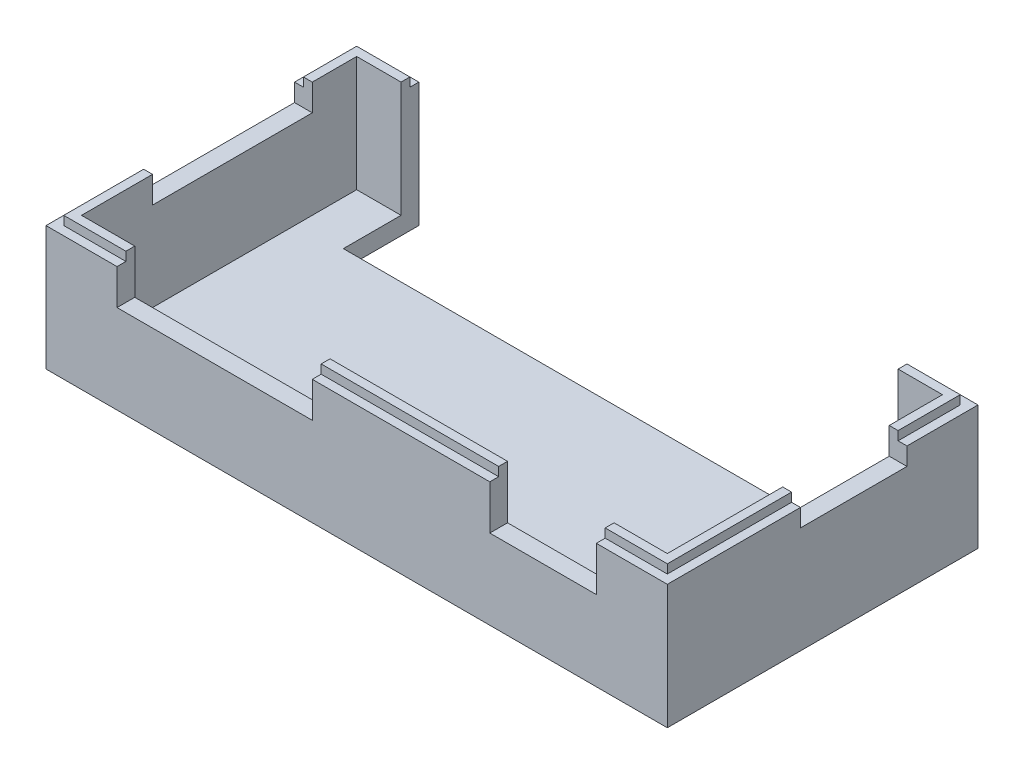
SolidWorks part; units mm, degrees
ref_plane "Front Plane" through (0, 0, 0) normal (0, 0, 1) x (1, 0, 0)
ref_plane "Top Plane" through (0, 0, 0) normal (0, 1, 0) x (1, 0, 0)
ref_plane "Right Plane" through (0, 0, 0) normal (1, 0, 0) x (0, 0, -1)
sketch "Sketch1" plane through (0, 0, 0) normal (0, 1, 0) x (1, 0, 0)
  line L0 (0, 0) -> (70, 0)
  line L1 (70, 0) -> (70, 35)
  line L2 (70, 35) -> (0, 35)
  line L3 (0, 35) -> (0, 0)
  dimension "D1" = 70
  dimension "D2" = 35
extrude "Boss-Extrude1" add sketch "Sketch1" along normal blind 2
sketch "Sketch2" plane through (0, 2, 0) normal (0, 1, 0) x (1, 0, 0)
  line L0 (68, 33) -> (2, 33)
  line L1 (2, 33) -> (2, 2)
  line L2 (2, 2) -> (68, 2)
  line L3 (68, 2) -> (68, 33)
  line L4 (0, 35) -> (0, 0)
  line L5 (0, 0) -> (70, 0)
  line L6 (70, 0) -> (70, 35)
  line L7 (70, 35) -> (0, 35)
  line L8 (0, 35) -> (0, 0)
  line L9 (0, 0) -> (70, 0)
  line L10 (70, 0) -> (70, 35)
  line L11 (70, 35) -> (0, 35)
  dimension "D1" = 0
  dimension "D2" = 2
extrude "Boss-Extrude2" add sketch "Sketch2" along normal blind 12
sketch "Sketch3" plane through (0, 2, 0) normal (0, 1, 0) x (1, 0, 0)
  line L0 (7, 35) -> (7, 26.5)
  line L1 (70, 35) -> (0, 35) construction
  line L2 (7, 26.5) -> (63, 26.5)
  line L3 (63, 26.5) -> (63, 35)
  line L4 (63, 35) -> (7, 35)
  line L5 (70, 0) -> (70, 35) construction
  dimension "D1" = 8.5
  dimension "D2" = 7
  dimension "D3" = 56
extrude "Cut-Extrude1" cut sketch "Sketch3" along normal blind 17 and the other way blind 15
sketch "Sketch4" plane through (68, 0, 0) normal (-1, 0, 0) x (0, 0, 1)
  line L0 (-27, 14) -> (-15, 14)
  line L1 (-35, 14) -> (0, 14) construction
  line L2 (-15, 14) -> (-15, 12)
  line L3 (-15, 12) -> (-27, 12)
  line L4 (-27, 12) -> (-27, 14)
  line L5 (-35, 14) -> (-35, 0) construction
  dimension "D1" = 2
  dimension "D2" = 8
  dimension "D3" = 12
extrude "Cut-Extrude2" cut sketch "Sketch4" against normal blind 17
sketch "Sketch5" plane through (0, 0, -2) normal (0, 0, -1) x (-1, 0, 0)
  line L1 (-2, 14) -> (-68, 14) construction
  line L15 (-35, -4.8424) -> (-35, 17.7446) construction
  line L16 (-8, 14) -> (-17, 14)
  line L17 (-8, 10) -> (-8, 14)
  line L18 (-17, 10) -> (-8, 10)
  line L19 (-17, 14) -> (-17, 10)
  line L20 (-21, 10) -> (-21, 14)
  line L21 (-21, 14) -> (-30, 14)
  line L22 (-30, 10) -> (-21, 10)
  line L23 (-30, 14) -> (-30, 10)
  line L24 (-62, 14) -> (-62, 9)
  line L25 (-62, 9) -> (-50, 9)
  line L26 (-50, 9) -> (-50, 14)
  line L27 (-50, 14) -> (-62, 14)
extrude "Cut-Extrude3" cut sketch "Sketch5" against normal blind 17
sketch "Sketch6" plane through (2, 0, 0) normal (1, 0, 0) x (0, 0, -1)
  line L0 (28, 14) -> (10, 14)
  line L1 (27, 14) -> (35, 14) construction
  line L2 (0, 14) -> (15, 14) construction
  line L3 (10, 14) -> (10, 12)
  line L4 (10, 12) -> (28, 12)
  line L5 (28, 12) -> (28, 14)
  line L6 (35, 14) -> (35, 0) construction
  dimension "D1" = 2
  dimension "D2" = 7
  dimension "D3" = 18
extrude "Cut-Extrude4" cut sketch "Sketch6" against normal blind 17
sketch "Sketch7" plane through (0, 14, 0) normal (0, 1, 0) x (1, 0, 0)
  line L10 (7, 33) -> (7, 34)
  line L11 (7, 35) -> (7, 33) construction
  line L12 (7, 34) -> (1, 34)
  line L13 (1, 34) -> (1, 28)
  line L14 (0, 28) -> (2, 28) construction
  line L15 (1, 28) -> (2, 28)
  line L16 (2, 28) -> (2, 33)
  line L17 (2, 33) -> (7, 33)
  line L18 (2, 10) -> (1, 10)
  line L19 (0, 10) -> (2, 10) construction
  line L20 (1, 10) -> (1, 1)
  line L21 (1, 1) -> (8, 1)
  line L23 (8, 0) -> (8, 2) construction
  line L24 (8, 1) -> (8, 2)
  line L25 (2, 2) -> (2, 10)
  line L26 (8, 2) -> (2, 2)
  line L28 (17, 2) -> (17, 1)
  line L30 (17, 0) -> (17, 2) construction
  line L31 (17, 1) -> (21, 1)
  line L32 (21, 0) -> (21, 2) construction
  line L34 (21, 1) -> (21, 2)
  line L36 (21, 2) -> (17, 2)
  line L38 (30, 2) -> (30, 1)
  line L39 (30, 0) -> (30, 2) construction
  line L41 (30, 1) -> (50, 1)
  line L42 (69, 1) -> (69, 15)
  line L43 (70, 15) -> (68, 15) construction
  line L44 (69, 15) -> (68, 15)
  line L45 (68, 15) -> (68, 2)
  line L46 (50, 0) -> (50, 2) construction
  line L47 (68, 27) -> (69, 27)
  line L48 (70, 27) -> (68, 27) construction
  line L49 (69, 27) -> (69, 34)
  line L50 (69, 34) -> (63, 34)
  line L51 (63, 33) -> (63, 35) construction
  line L52 (63, 34) -> (63, 33)
  line L53 (63, 33) -> (68, 33)
  line L54 (68, 33) -> (68, 27)
  line L55 (50, 1) -> (50, 2)
  line L56 (50, 2) -> (30, 2)
  line L57 (68, 2) -> (62, 2)
  line L58 (62, 2) -> (62, 1)
  line L59 (62, 0) -> (62, 2) construction
  line L60 (62, 1) -> (69, 1)
extrude "Boss-Extrude4" add sketch "Sketch7" along normal blind 1
sketch "Sketch8" plane through (0, 0, -2) normal (0, 0, -1) x (-1, 0, 0)
  line L0 (-21, 15) -> (-21, 10)
  line L1 (-21, 10) -> (-17, 10)
  line L2 (-17, 10) -> (-17, 15)
  line L3 (-17, 15) -> (-21, 15)
extrude "Cut-Extrude5" cut sketch "Sketch8" against normal blind 3
